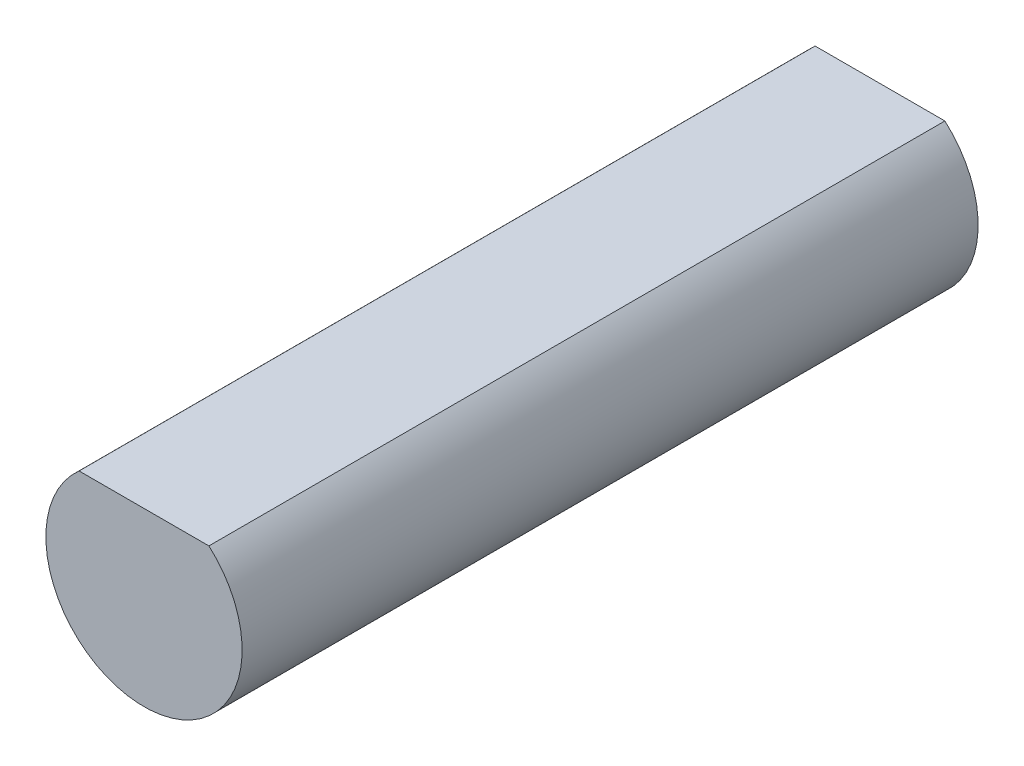
SolidWorks part; units mm, degrees
ref_plane "Front Plane" through (0, 0, 0) normal (0, 0, 1) x (1, 0, 0)
ref_plane "Top Plane" through (0, 0, 0) normal (0, 1, 0) x (1, 0, 0)
ref_plane "Right Plane" through (0, 0, 0) normal (1, 0, 0) x (0, 0, -1)
sketch "Sketch1" plane through (0, 0, 0) normal (0, 0, 1) x (1, 0, 0)
  line L0 (1.3229, 1.5) -> (-1.3229, 1.5)
  arc A0 (-1.3229, 1.5) -> (1.3229, 1.5) centre (0, 0) ccw
  dimension "D1" = 4
  dimension "D2" = 1.5
extrude "Boss-Extrude1" add sketch "Sketch1" against normal blind 15
equation "\"height\"= 15"
equation "\"D1@Boss-Extrude1\"= \"height\""
